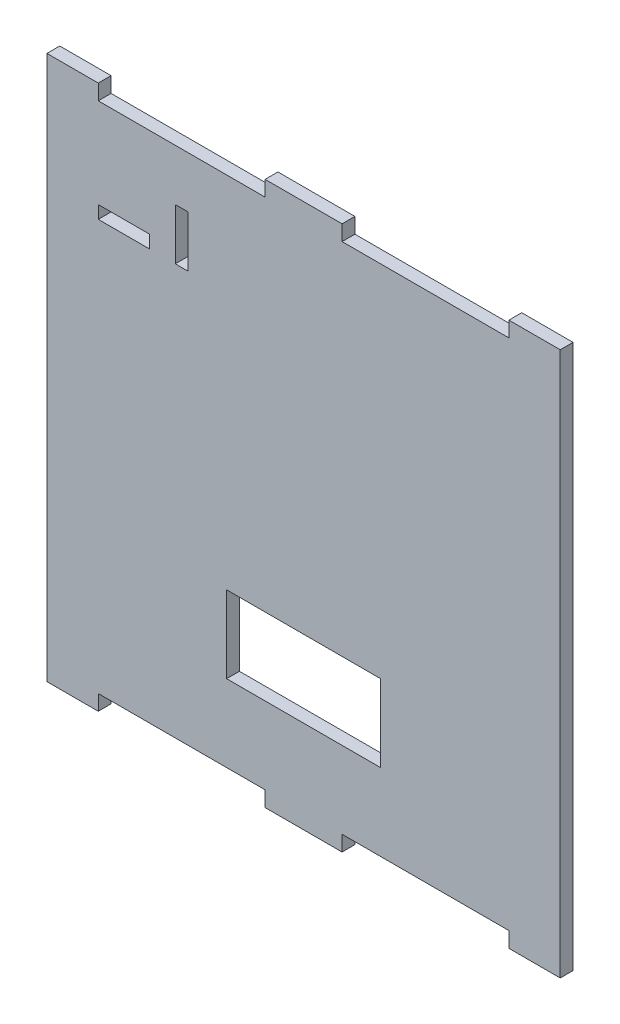
SolidWorks part; units mm, degrees
ref_plane "Plan de face" through (0, 0, 0) normal (0, 0, 1) x (1, 0, 0)
ref_plane "Plan de dessus" through (0, 0, 0) normal (0, 1, 0) x (1, 0, 0)
ref_plane "Plan de droite" through (0, 0, 0) normal (1, 0, 0) x (0, 0, -1)
sketch "Esquisse1" plane through (0, 0, 0) normal (0, 0, 1) x (1, 0, 0)
  line L0 (0, 0) -> (0, 212)
  line L1 (0, 212) -> (20, 212)
  line L2 (20, 212) -> (20, 206)
  line L3 (20, 206) -> (85, 206)
  line L4 (180, 206) -> (180, 212)
  line L5 (180, 212) -> (200, 212)
  line L6 (200, 212) -> (200, 0)
  line L7 (200, 0) -> (180, 0)
  line L8 (180, 0) -> (180, 6)
  line L9 (85, 212) -> (115, 212)
  line L10 (20, 6) -> (20, 0)
  line L11 (20, 0) -> (0, 0)
  line L12 (115, 212) -> (115, 206)
  line L13 (115, 206) -> (180, 206)
  line L14 (20, 6) -> (85, 6)
  line L15 (85, 6) -> (85, 0)
  line L16 (85, 0) -> (115, 0)
  line L17 (115, 0) -> (115, 6)
  line L18 (115, 6) -> (180, 6)
  line L19 (85, 206) -> (85, 212)
  line L21 (70, 66) -> (130, 66)
  line L22 (70, 66) -> (70, 36)
  line L23 (70, 36) -> (130, 36)
  line L24 (130, 66) -> (130, 36)
  line L25 (20, 166) -> (40, 166)
  line L26 (20, 166) -> (20, 171)
  line L27 (20, 171) -> (40, 171)
  line L28 (40, 166) -> (40, 171)
  line L29 (50, 186) -> (55, 186)
  line L30 (50, 186) -> (50, 166)
  line L31 (50, 166) -> (55, 166)
  line L32 (55, 186) -> (55, 166)
  point P33 (40, 168.5)
  dimension "D1" = 20
  dimension "D2" = 20
  dimension "D3" = 200
  dimension "D4" = 200
  dimension "D5" = 60
  dimension "D6" = 6
  dimension "D7" = 6
  dimension "D8" = 20
  dimension "D9" = 30
  dimension "D10" = 30
  dimension "D11" = 6
  dimension "D12" = 6
  dimension "D13" = 65
  dimension "D14" = 65
  dimension "D15" = 30
  dimension "D16" = 70
  dimension "D17" = 30
  dimension "D18" = 20
  dimension "D19" = 20
  dimension "D20" = 5
  dimension "D21" = 5
  dimension "D22" = 10
  dimension "D23" = 35
  dimension "D25" = 20
extrude "Boss.-Extru.1" add sketch "Esquisse1" along normal blind 5
